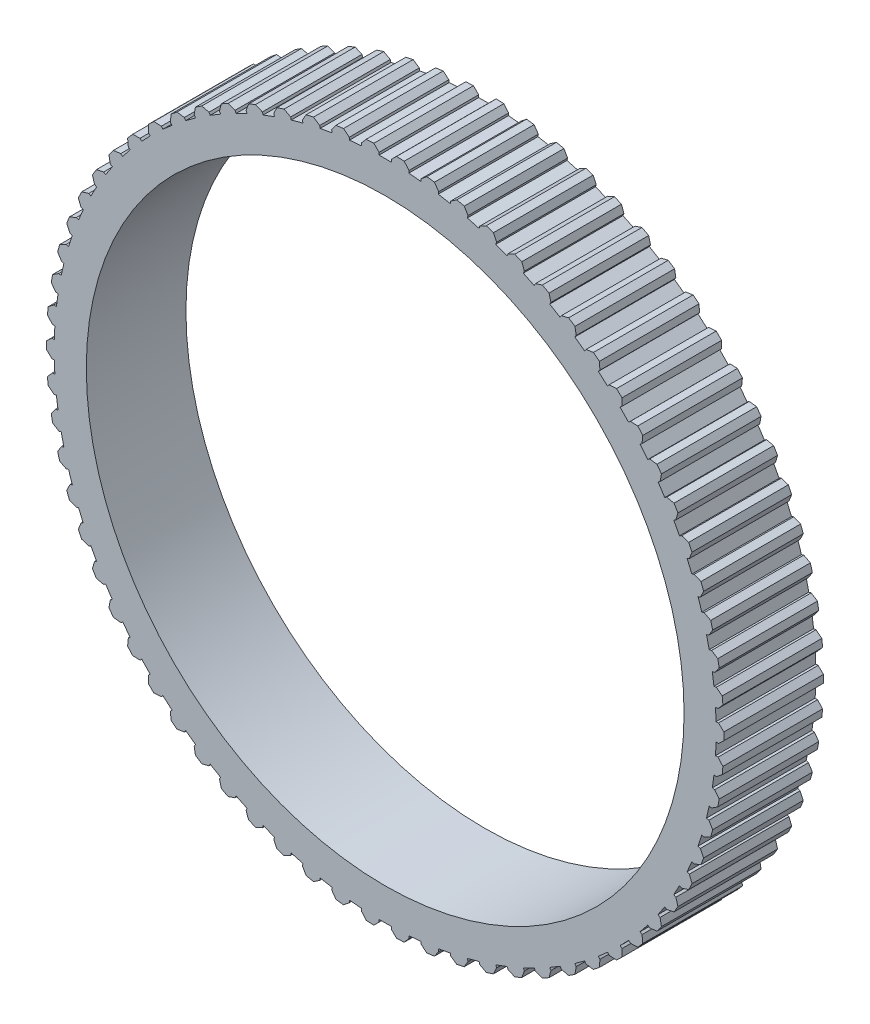
SolidWorks part; units mm, degrees
ref_plane "Front Plane" through (0, 0, 0) normal (0, 0, 1) x (1, 0, 0)
ref_plane "Top Plane" through (0, 0, 0) normal (0, 1, 0) x (1, 0, 0)
ref_plane "Right Plane" through (0, 0, 0) normal (1, 0, 0) x (0, 0, -1)
sketch "Sketch1" plane through (0, 0, 0) normal (0, 0, 1) x (1, 0, 0)
  line L0 (-2.86, 50.9197) -> (-3.5866, 50.0718)
  line L1 (-3.5866, 50.0718) -> (-3.5538, 49.707)
  line L2 (-3.5538, 49.707) -> (-5.3789, 49.5427)
  line L3 (-5.3789, 49.5427) -> (-5.4117, 49.9076)
  line L4 (-5.4117, 49.9076) -> (-6.2781, 50.6121)
  line L5 (-7.4129, 50.4584) -> (-8.0606, 49.5488)
  line L6 (-8.0606, 49.5488) -> (-7.9952, 49.1883)
  line L7 (-7.9952, 49.1883) -> (-9.7982, 48.8611)
  line L8 (-9.7982, 48.8611) -> (-9.8636, 49.2216)
  line L9 (-9.8636, 49.2216) -> (-10.7896, 49.8456)
  line L10 (-11.9061, 49.5908) -> (-12.4696, 48.6268)
  line L11 (-12.4696, 48.6268) -> (-12.3722, 48.2736)
  line L12 (-12.3722, 48.2736) -> (-14.1386, 47.7861)
  line L13 (-14.1386, 47.7861) -> (-14.2361, 48.1393)
  line L14 (-14.2361, 48.1393) -> (-15.2143, 48.6778)
  line L15 (-16.3034, 48.3239) -> (-16.7783, 47.3132)
  line L16 (-16.7783, 47.3132) -> (-16.6496, 46.9703)
  line L17 (-16.6496, 46.9703) -> (-18.3652, 46.3264)
  line L18 (-18.3652, 46.3264) -> (-18.4939, 46.6693)
  line L19 (-18.4939, 46.6693) -> (-19.5165, 47.118)
  line L20 (-20.5695, 46.6679) -> (-20.9519, 45.6188)
  line L21 (-20.9519, 45.6188) -> (-20.793, 45.2887)
  line L22 (-20.793, 45.2887) -> (-22.444, 44.4937)
  line L23 (-22.444, 44.4937) -> (-22.6029, 44.8237)
  line L24 (-22.6029, 44.8237) -> (-23.6616, 45.1789)
  line L25 (-24.67, 44.6362) -> (-24.9568, 43.557)
  line L26 (-24.9568, 43.557) -> (-24.7689, 43.2425)
  line L27 (-24.7689, 43.2425) -> (-26.342, 42.3027)
  line L28 (-26.342, 42.3027) -> (-26.5299, 42.6171)
  line L29 (-26.5299, 42.6171) -> (-27.6161, 42.876)
  line L30 (-28.5718, 42.2451) -> (-28.7607, 41.1445)
  line L31 (-28.7607, 41.1445) -> (-28.5454, 40.8482)
  line L32 (-28.5454, 40.8482) -> (-30.0279, 39.7711)
  line L33 (-30.0279, 39.7711) -> (-30.2432, 40.0674)
  line L34 (-30.2432, 40.0674) -> (-31.3483, 40.2279)
  line L35 (-32.2436, 39.5139) -> (-32.3331, 38.4008)
  line L36 (-32.3331, 38.4008) -> (-32.0921, 38.125)
  line L37 (-32.0921, 38.125) -> (-33.4721, 36.9193)
  line L38 (-33.4721, 36.9193) -> (-33.7131, 37.1952)
  line L39 (-33.7131, 37.1952) -> (-34.8281, 37.2559)
  line L40 (-35.6558, 36.4645) -> (-35.6452, 35.3479)
  line L41 (-35.6452, 35.3479) -> (-35.3804, 35.0948)
  line L42 (-35.3804, 35.0948) -> (-36.6468, 33.7703)
  line L43 (-36.6468, 33.7703) -> (-36.9115, 34.0234)
  line L44 (-36.9115, 34.0234) -> (-38.0275, 33.9839)
  line L45 (-38.7809, 33.1216) -> (-38.6702, 32.0104)
  line L46 (-38.6702, 32.0104) -> (-38.3839, 31.782)
  line L47 (-38.3839, 31.782) -> (-39.5264, 30.3493)
  line L48 (-39.5264, 30.3493) -> (-39.8128, 30.5777)
  line L49 (-39.8128, 30.5777) -> (-40.9207, 30.4384)
  line L50 (-41.5938, 29.5119) -> (-41.384, 28.4152)
  line L51 (-41.384, 28.4152) -> (-41.0782, 28.2134)
  line L52 (-41.0782, 28.2134) -> (-42.0877, 26.684)
  line L53 (-42.0877, 26.684) -> (-42.3935, 26.8858)
  line L54 (-42.3935, 26.8858) -> (-43.4845, 26.6477)
  line L55 (-44.0718, 25.6647) -> (-43.7645, 24.5911)
  line L56 (-43.7645, 24.5911) -> (-43.4419, 24.4176)
  line L57 (-43.4419, 24.4176) -> (-44.3103, 22.8039)
  line L58 (-44.3103, 22.8039) -> (-44.6328, 22.9775)
  line L59 (-44.6328, 22.9775) -> (-45.6981, 22.6425)
  line L60 (-46.1949, 21.6108) -> (-45.7926, 20.5691)
  line L61 (-45.7926, 20.5691) -> (-45.4558, 20.4252)
  line L62 (-45.4558, 20.4252) -> (-46.176, 18.7402)
  line L63 (-46.176, 18.7402) -> (-46.5128, 18.8841)
  line L64 (-46.5128, 18.8841) -> (-47.5438, 18.4551)
  line L65 (-47.9462, 17.3829) -> (-47.4521, 16.3815)
  line L66 (-47.4521, 16.3815) -> (-47.1037, 16.2683)
  line L67 (-47.1037, 16.2683) -> (-47.67, 14.5255)
  line L68 (-47.67, 14.5255) -> (-48.0183, 14.6387)
  line L69 (-48.0183, 14.6387) -> (-49.0067, 14.119)
  line L70 (-49.3113, 13.0151) -> (-48.7295, 12.062)
  line L71 (-48.7295, 12.062) -> (-48.3724, 11.9805)
  line L72 (-48.3724, 11.9805) -> (-48.7801, 10.1939)
  line L73 (-48.7801, 10.1939) -> (-49.1372, 10.2755)
  line L74 (-49.1372, 10.2755) -> (-50.075, 9.6692)
  line L75 (-50.2795, 8.5425) -> (-49.6145, 7.6453)
  line L76 (-49.6145, 7.6453) -> (-49.2515, 7.5962)
  line L77 (-49.2515, 7.5962) -> (-49.4975, 5.7803)
  line L78 (-49.4975, 5.7803) -> (-49.8605, 5.8295)
  line L79 (-49.8605, 5.8295) -> (-50.7402, 5.1416)
  line L80 (-50.8428, 4.001) -> (-50.1001, 3.1672)
  line L81 (-50.1001, 3.1672) -> (-49.7342, 3.1507)
  line L82 (-49.7342, 3.1507) -> (-49.8164, 1.3201)
  line L83 (-49.8164, 1.3201) -> (-50.1823, 1.3365)
  line L84 (-50.1823, 1.3365) -> (-50.9968, 0.5726)
  line L85 (-50.9968, -0.5726) -> (-50.1823, -1.3365)
  line L86 (-50.1823, -1.3365) -> (-49.8164, -1.3201)
  line L87 (-49.8164, -1.3201) -> (-49.7342, -3.1507)
  line L88 (-49.7342, -3.1507) -> (-50.1001, -3.1672)
  line L89 (-50.1001, -3.1672) -> (-50.8428, -4.001)
  line L90 (-50.7402, -5.1416) -> (-49.8605, -5.8295)
  line L91 (-49.8605, -5.8295) -> (-49.4975, -5.7803)
  line L92 (-49.4975, -5.7803) -> (-49.2515, -7.5962)
  line L93 (-49.2515, -7.5962) -> (-49.6145, -7.6453)
  line L94 (-49.6145, -7.6453) -> (-50.2795, -8.5425)
  line L95 (-50.075, -9.6692) -> (-49.1372, -10.2755)
  line L96 (-49.1372, -10.2755) -> (-48.7801, -10.1939)
  line L97 (-48.7801, -10.1939) -> (-48.3724, -11.9805)
  line L98 (-48.3724, -11.9805) -> (-48.7295, -12.062)
  line L99 (-48.7295, -12.062) -> (-49.3113, -13.0151)
  line L100 (-49.0067, -14.119) -> (-48.0183, -14.6387)
  line L101 (-48.0183, -14.6387) -> (-47.67, -14.5255)
  line L102 (-47.67, -14.5255) -> (-47.1037, -16.2683)
  line L103 (-47.1037, -16.2683) -> (-47.4521, -16.3815)
  line L104 (-47.4521, -16.3815) -> (-47.9462, -17.3829)
  line L105 (-47.5438, -18.4551) -> (-46.5128, -18.8841)
  line L106 (-46.5128, -18.8841) -> (-46.176, -18.7402)
  line L107 (-46.176, -18.7402) -> (-45.4558, -20.4252)
  line L108 (-45.4558, -20.4252) -> (-45.7926, -20.5691)
  line L109 (-45.7926, -20.5691) -> (-46.1949, -21.6108)
  line L110 (-45.6981, -22.6425) -> (-44.6328, -22.9775)
  line L111 (-44.6328, -22.9775) -> (-44.3103, -22.8039)
  line L112 (-44.3103, -22.8039) -> (-43.4419, -24.4176)
  line L113 (-43.4419, -24.4176) -> (-43.7645, -24.5911)
  line L114 (-43.7645, -24.5911) -> (-44.0718, -25.6647)
  line L115 (-43.4845, -26.6477) -> (-42.3935, -26.8858)
  line L116 (-42.3935, -26.8858) -> (-42.0877, -26.684)
  line L117 (-42.0877, -26.684) -> (-41.0782, -28.2134)
  line L118 (-41.0782, -28.2134) -> (-41.384, -28.4152)
  line L119 (-41.384, -28.4152) -> (-41.5938, -29.5119)
  line L120 (-40.9207, -30.4384) -> (-39.8128, -30.5777)
  line L121 (-39.8128, -30.5777) -> (-39.5264, -30.3493)
  line L122 (-39.5264, -30.3493) -> (-38.3839, -31.782)
  line L123 (-38.3839, -31.782) -> (-38.6702, -32.0104)
  line L124 (-38.6702, -32.0104) -> (-38.7809, -33.1216)
  line L125 (-38.0275, -33.9839) -> (-36.9115, -34.0234)
  line L126 (-36.9115, -34.0234) -> (-36.6468, -33.7703)
  line L127 (-36.6468, -33.7703) -> (-35.3804, -35.0948)
  line L128 (-35.3804, -35.0948) -> (-35.6452, -35.3479)
  line L129 (-35.6452, -35.3479) -> (-35.6558, -36.4645)
  line L130 (-34.8281, -37.2559) -> (-33.7131, -37.1952)
  line L131 (-33.7131, -37.1952) -> (-33.4721, -36.9193)
  line L132 (-33.4721, -36.9193) -> (-32.0921, -38.125)
  line L133 (-32.0921, -38.125) -> (-32.3331, -38.4008)
  line L134 (-32.3331, -38.4008) -> (-32.2436, -39.5139)
  line L135 (-31.3483, -40.2279) -> (-30.2432, -40.0674)
  line L136 (-30.2432, -40.0674) -> (-30.0279, -39.7711)
  line L137 (-30.0279, -39.7711) -> (-28.5454, -40.8482)
  line L138 (-28.5454, -40.8482) -> (-28.7607, -41.1445)
  line L139 (-28.7607, -41.1445) -> (-28.5718, -42.2451)
  line L140 (-27.6161, -42.876) -> (-26.5299, -42.6171)
  line L141 (-26.5299, -42.6171) -> (-26.342, -42.3027)
  line L142 (-26.342, -42.3027) -> (-24.7689, -43.2425)
  line L143 (-24.7689, -43.2425) -> (-24.9568, -43.557)
  line L144 (-24.9568, -43.557) -> (-24.67, -44.6362)
  line L145 (-23.6616, -45.1789) -> (-22.6029, -44.8237)
  line L146 (-22.6029, -44.8237) -> (-22.444, -44.4937)
  line L147 (-22.444, -44.4937) -> (-20.793, -45.2887)
  line L148 (-20.793, -45.2887) -> (-20.9519, -45.6188)
  line L149 (-20.9519, -45.6188) -> (-20.5695, -46.6679)
  line L150 (-19.5165, -47.118) -> (-18.4939, -46.6693)
  line L151 (-18.4939, -46.6693) -> (-18.3652, -46.3264)
  line L152 (-18.3652, -46.3264) -> (-16.6496, -46.9703)
  line L153 (-16.6496, -46.9703) -> (-16.7783, -47.3132)
  line L154 (-16.7783, -47.3132) -> (-16.3034, -48.3239)
  line L155 (-15.2143, -48.6778) -> (-14.2361, -48.1393)
  line L156 (-14.2361, -48.1393) -> (-14.1386, -47.7861)
  line L157 (-14.1386, -47.7861) -> (-12.3722, -48.2736)
  line L158 (-12.3722, -48.2736) -> (-12.4696, -48.6268)
  line L159 (-12.4696, -48.6268) -> (-11.9061, -49.5908)
  line L160 (-10.7896, -49.8456) -> (-9.8636, -49.2216)
  line L161 (-9.8636, -49.2216) -> (-9.7982, -48.8611)
  line L162 (-9.7982, -48.8611) -> (-7.9952, -49.1883)
  line L163 (-7.9952, -49.1883) -> (-8.0606, -49.5488)
  line L164 (-8.0606, -49.5488) -> (-7.4129, -50.4584)
  line L165 (-6.2781, -50.6121) -> (-5.4117, -49.9076)
  line L166 (-5.4117, -49.9076) -> (-5.3789, -49.5427)
  line L167 (-5.3789, -49.5427) -> (-3.5538, -49.707)
  line L168 (-3.5538, -49.707) -> (-3.5866, -50.0718)
  line L169 (-3.5866, -50.0718) -> (-2.86, -50.9197)
  line L170 (-1.716, -50.9711) -> (-0.9162, -50.1918)
  line L171 (-0.9162, -50.1918) -> (-0.9162, -49.8255)
  line L172 (-0.9162, -49.8255) -> (0.9162, -49.8255)
  line L173 (0.9162, -49.8255) -> (0.9162, -50.1918)
  line L174 (0.9162, -50.1918) -> (1.716, -50.9711)
  line L175 (2.86, -50.9197) -> (3.5866, -50.0718)
  line L176 (3.5866, -50.0718) -> (3.5538, -49.707)
  line L177 (3.5538, -49.707) -> (5.3789, -49.5427)
  line L178 (5.3789, -49.5427) -> (5.4117, -49.9076)
  line L179 (5.4117, -49.9076) -> (6.2781, -50.6121)
  line L180 (7.4129, -50.4584) -> (8.0606, -49.5488)
  line L181 (8.0606, -49.5488) -> (7.9952, -49.1883)
  line L182 (7.9952, -49.1883) -> (9.7982, -48.8611)
  line L183 (9.7982, -48.8611) -> (9.8636, -49.2216)
  line L184 (9.8636, -49.2216) -> (10.7896, -49.8456)
  line L185 (11.9061, -49.5908) -> (12.4696, -48.6268)
  line L186 (12.4696, -48.6268) -> (12.3722, -48.2736)
  line L187 (12.3722, -48.2736) -> (14.1386, -47.7861)
  line L188 (14.1386, -47.7861) -> (14.2361, -48.1393)
  line L189 (14.2361, -48.1393) -> (15.2143, -48.6778)
  line L190 (16.3034, -48.3239) -> (16.7783, -47.3132)
  line L191 (16.7783, -47.3132) -> (16.6496, -46.9703)
  line L192 (16.6496, -46.9703) -> (18.3652, -46.3264)
  line L193 (18.3652, -46.3264) -> (18.4939, -46.6693)
  line L194 (18.4939, -46.6693) -> (19.5165, -47.118)
  line L195 (20.5695, -46.6679) -> (20.9519, -45.6188)
  line L196 (20.9519, -45.6188) -> (20.793, -45.2887)
  line L197 (20.793, -45.2887) -> (22.444, -44.4937)
  line L198 (22.444, -44.4937) -> (22.6029, -44.8237)
  line L199 (22.6029, -44.8237) -> (23.6616, -45.1789)
  line L200 (24.67, -44.6362) -> (24.9568, -43.557)
  line L201 (24.9568, -43.557) -> (24.7689, -43.2425)
  line L202 (24.7689, -43.2425) -> (26.342, -42.3027)
  line L203 (26.342, -42.3027) -> (26.5299, -42.6171)
  line L204 (26.5299, -42.6171) -> (27.6161, -42.876)
  line L205 (28.5718, -42.2451) -> (28.7607, -41.1445)
  line L206 (28.7607, -41.1445) -> (28.5454, -40.8482)
  line L207 (28.5454, -40.8482) -> (30.0279, -39.7711)
  line L208 (30.0279, -39.7711) -> (30.2432, -40.0674)
  line L209 (30.2432, -40.0674) -> (31.3483, -40.2279)
  line L210 (32.2436, -39.5139) -> (32.3331, -38.4008)
  line L211 (32.3331, -38.4008) -> (32.0921, -38.125)
  line L212 (32.0921, -38.125) -> (33.4721, -36.9193)
  line L213 (33.4721, -36.9193) -> (33.7131, -37.1952)
  line L214 (33.7131, -37.1952) -> (34.8281, -37.2559)
  line L215 (35.6558, -36.4645) -> (35.6452, -35.3479)
  line L216 (35.6452, -35.3479) -> (35.3804, -35.0948)
  line L217 (35.3804, -35.0948) -> (36.6468, -33.7703)
  line L218 (36.6468, -33.7703) -> (36.9115, -34.0234)
  line L219 (36.9115, -34.0234) -> (38.0275, -33.9839)
  line L220 (38.7809, -33.1216) -> (38.6702, -32.0104)
  line L221 (38.6702, -32.0104) -> (38.3839, -31.782)
  line L222 (38.3839, -31.782) -> (39.5264, -30.3493)
  line L223 (39.5264, -30.3493) -> (39.8128, -30.5777)
  line L224 (39.8128, -30.5777) -> (40.9207, -30.4384)
  line L225 (41.5938, -29.5119) -> (41.384, -28.4152)
  line L226 (41.384, -28.4152) -> (41.0782, -28.2134)
  line L227 (41.0782, -28.2134) -> (42.0877, -26.684)
  line L228 (42.0877, -26.684) -> (42.3935, -26.8858)
  line L229 (42.3935, -26.8858) -> (43.4845, -26.6477)
  line L230 (44.0718, -25.6647) -> (43.7645, -24.5911)
  line L231 (43.7645, -24.5911) -> (43.4419, -24.4176)
  line L232 (43.4419, -24.4176) -> (44.3103, -22.8039)
  line L233 (44.3103, -22.8039) -> (44.6328, -22.9775)
  line L234 (44.6328, -22.9775) -> (45.6981, -22.6425)
  line L235 (46.1949, -21.6108) -> (45.7926, -20.5691)
  line L236 (45.7926, -20.5691) -> (45.4558, -20.4252)
  line L237 (45.4558, -20.4252) -> (46.176, -18.7402)
  line L238 (46.176, -18.7402) -> (46.5128, -18.8841)
  line L239 (46.5128, -18.8841) -> (47.5438, -18.4551)
  line L240 (47.9462, -17.3829) -> (47.4521, -16.3815)
  line L241 (47.4521, -16.3815) -> (47.1037, -16.2683)
  line L242 (47.1037, -16.2683) -> (47.67, -14.5255)
  line L243 (47.67, -14.5255) -> (48.0183, -14.6387)
  line L244 (48.0183, -14.6387) -> (49.0067, -14.119)
  line L245 (49.3113, -13.0151) -> (48.7295, -12.062)
  line L246 (48.7295, -12.062) -> (48.3724, -11.9805)
  line L247 (48.3724, -11.9805) -> (48.7801, -10.1939)
  line L248 (48.7801, -10.1939) -> (49.1372, -10.2755)
  line L249 (49.1372, -10.2755) -> (50.075, -9.6692)
  line L250 (50.2795, -8.5425) -> (49.6145, -7.6453)
  line L251 (49.6145, -7.6453) -> (49.2515, -7.5962)
  line L252 (49.2515, -7.5962) -> (49.4975, -5.7803)
  line L253 (49.4975, -5.7803) -> (49.8605, -5.8295)
  line L254 (49.8605, -5.8295) -> (50.7402, -5.1416)
  line L255 (50.8428, -4.001) -> (50.1001, -3.1672)
  line L256 (50.1001, -3.1672) -> (49.7342, -3.1507)
  line L257 (49.7342, -3.1507) -> (49.8164, -1.3201)
  line L258 (49.8164, -1.3201) -> (50.1823, -1.3365)
  line L259 (50.1823, -1.3365) -> (50.9968, -0.5726)
  line L260 (50.9968, 0.5726) -> (50.1823, 1.3365)
  line L261 (50.1823, 1.3365) -> (49.8164, 1.3201)
  line L262 (49.8164, 1.3201) -> (49.7342, 3.1507)
  line L263 (49.7342, 3.1507) -> (50.1001, 3.1672)
  line L264 (50.1001, 3.1672) -> (50.8428, 4.001)
  line L265 (50.7402, 5.1416) -> (49.8605, 5.8295)
  line L266 (49.8605, 5.8295) -> (49.4975, 5.7803)
  line L267 (49.4975, 5.7803) -> (49.2515, 7.5962)
  line L268 (49.2515, 7.5962) -> (49.6145, 7.6453)
  line L269 (49.6145, 7.6453) -> (50.2795, 8.5425)
  line L270 (50.075, 9.6692) -> (49.1372, 10.2755)
  line L271 (49.1372, 10.2755) -> (48.7801, 10.1939)
  line L272 (48.7801, 10.1939) -> (48.3724, 11.9805)
  line L273 (48.3724, 11.9805) -> (48.7295, 12.062)
  line L274 (48.7295, 12.062) -> (49.3113, 13.0151)
  line L275 (49.0067, 14.119) -> (48.0183, 14.6387)
  line L276 (48.0183, 14.6387) -> (47.67, 14.5255)
  line L277 (47.67, 14.5255) -> (47.1037, 16.2683)
  line L278 (47.1037, 16.2683) -> (47.4521, 16.3815)
  line L279 (47.4521, 16.3815) -> (47.9462, 17.3829)
  line L280 (47.5438, 18.4551) -> (46.5128, 18.8841)
  line L281 (46.5128, 18.8841) -> (46.176, 18.7402)
  line L282 (46.176, 18.7402) -> (45.4558, 20.4252)
  line L283 (45.4558, 20.4252) -> (45.7926, 20.5691)
  line L284 (45.7926, 20.5691) -> (46.1949, 21.6108)
  line L285 (45.6981, 22.6425) -> (44.6328, 22.9775)
  line L286 (44.6328, 22.9775) -> (44.3103, 22.8039)
  line L287 (44.3103, 22.8039) -> (43.4419, 24.4176)
  line L288 (43.4419, 24.4176) -> (43.7645, 24.5911)
  line L289 (43.7645, 24.5911) -> (44.0718, 25.6647)
  line L290 (43.4845, 26.6477) -> (42.3935, 26.8858)
  line L291 (42.3935, 26.8858) -> (42.0877, 26.684)
  line L292 (42.0877, 26.684) -> (41.0782, 28.2134)
  line L293 (41.0782, 28.2134) -> (41.384, 28.4152)
  line L294 (41.384, 28.4152) -> (41.5938, 29.5119)
  line L295 (40.9207, 30.4384) -> (39.8128, 30.5777)
  line L296 (39.8128, 30.5777) -> (39.5264, 30.3493)
  line L297 (39.5264, 30.3493) -> (38.3839, 31.782)
  line L298 (38.3839, 31.782) -> (38.6702, 32.0104)
  line L299 (38.6702, 32.0104) -> (38.7809, 33.1216)
  line L300 (38.0275, 33.9839) -> (36.9115, 34.0234)
  line L301 (36.9115, 34.0234) -> (36.6468, 33.7703)
  line L302 (36.6468, 33.7703) -> (35.3804, 35.0948)
  line L303 (35.3804, 35.0948) -> (35.6452, 35.3479)
  line L304 (35.6452, 35.3479) -> (35.6558, 36.4645)
  line L305 (34.8281, 37.2559) -> (33.7131, 37.1952)
  line L306 (33.7131, 37.1952) -> (33.4721, 36.9193)
  line L307 (33.4721, 36.9193) -> (32.0921, 38.125)
  line L308 (32.0921, 38.125) -> (32.3331, 38.4008)
  line L309 (32.3331, 38.4008) -> (32.2436, 39.5139)
  line L310 (31.3483, 40.2279) -> (30.2432, 40.0674)
  line L311 (30.2432, 40.0674) -> (30.0279, 39.7711)
  line L312 (30.0279, 39.7711) -> (28.5454, 40.8482)
  line L313 (28.5454, 40.8482) -> (28.7607, 41.1445)
  line L314 (28.7607, 41.1445) -> (28.5718, 42.2451)
  line L315 (27.6161, 42.876) -> (26.5299, 42.6171)
  line L316 (26.5299, 42.6171) -> (26.342, 42.3027)
  line L317 (26.342, 42.3027) -> (24.7689, 43.2425)
  line L318 (24.7689, 43.2425) -> (24.9568, 43.557)
  line L319 (24.9568, 43.557) -> (24.67, 44.6362)
  line L320 (23.6616, 45.1789) -> (22.6029, 44.8237)
  line L321 (22.6029, 44.8237) -> (22.444, 44.4937)
  line L322 (22.444, 44.4937) -> (20.793, 45.2887)
  line L323 (20.793, 45.2887) -> (20.9519, 45.6188)
  line L324 (20.9519, 45.6188) -> (20.5695, 46.6679)
  line L325 (19.5165, 47.118) -> (18.4939, 46.6693)
  line L326 (18.4939, 46.6693) -> (18.3652, 46.3264)
  line L327 (18.3652, 46.3264) -> (16.6496, 46.9703)
  line L328 (16.6496, 46.9703) -> (16.7783, 47.3132)
  line L329 (16.7783, 47.3132) -> (16.3034, 48.3239)
  line L330 (15.2143, 48.6778) -> (14.2361, 48.1393)
  line L331 (14.2361, 48.1393) -> (14.1386, 47.7861)
  line L332 (14.1386, 47.7861) -> (12.3722, 48.2736)
  line L333 (12.3722, 48.2736) -> (12.4696, 48.6268)
  line L334 (12.4696, 48.6268) -> (11.9061, 49.5908)
  line L335 (10.7896, 49.8456) -> (9.8636, 49.2216)
  line L336 (9.8636, 49.2216) -> (9.7982, 48.8611)
  line L337 (9.7982, 48.8611) -> (7.9952, 49.1883)
  line L338 (7.9952, 49.1883) -> (8.0606, 49.5488)
  line L339 (8.0606, 49.5488) -> (7.4129, 50.4584)
  line L340 (6.2781, 50.6121) -> (5.4117, 49.9076)
  line L341 (5.4117, 49.9076) -> (5.3789, 49.5427)
  line L342 (5.3789, 49.5427) -> (3.5538, 49.707)
  line L343 (3.5538, 49.707) -> (3.5866, 50.0718)
  line L344 (3.5866, 50.0718) -> (2.86, 50.9197)
  line L345 (1.716, 50.9711) -> (0.9162, 50.1918)
  line L346 (0.9162, 50.1918) -> (0.9162, 49.8255)
  line L347 (0.9162, 49.8255) -> (-0.9162, 49.8255)
  line L348 (-0.9162, 49.8255) -> (-0.9162, 50.1918)
  line L349 (-0.9162, 50.1918) -> (-1.716, 50.9711)
  circle A0 centre (0, 0) radius 45
  arc A1 (-6.2781, 50.6121) -> (-7.4129, 50.4584) centre (0, 0) ccw
  arc A2 (-10.7896, 49.8456) -> (-11.9061, 49.5908) centre (0, 0) ccw
  arc A3 (-15.2143, 48.6778) -> (-16.3034, 48.3239) centre (0, 0) ccw
  arc A4 (-19.5165, 47.118) -> (-20.5695, 46.6679) centre (0, 0) ccw
  arc A5 (-23.6616, 45.1789) -> (-24.67, 44.6362) centre (0, 0) ccw
  arc A6 (-27.6161, 42.876) -> (-28.5718, 42.2451) centre (0, 0) ccw
  arc A7 (-31.3483, 40.2279) -> (-32.2436, 39.5139) centre (0, 0) ccw
  arc A8 (-34.8281, 37.2559) -> (-35.6558, 36.4645) centre (0, 0) ccw
  arc A9 (-38.0275, 33.9839) -> (-38.7809, 33.1216) centre (0, 0) ccw
  arc A10 (-40.9207, 30.4384) -> (-41.5938, 29.5119) centre (0, 0) ccw
  arc A11 (-43.4845, 26.6477) -> (-44.0718, 25.6647) centre (0, 0) ccw
  arc A12 (-45.6981, 22.6425) -> (-46.1949, 21.6108) centre (0, 0) ccw
  arc A13 (-47.5438, 18.4551) -> (-47.9462, 17.3829) centre (0, 0) ccw
  arc A14 (-49.0067, 14.119) -> (-49.3113, 13.0151) centre (0, 0) ccw
  arc A15 (-50.075, 9.6692) -> (-50.2795, 8.5425) centre (0, 0) ccw
  arc A16 (-50.7402, 5.1416) -> (-50.8428, 4.001) centre (0, 0) ccw
  arc A17 (-50.9968, 0.5726) -> (-50.9968, -0.5726) centre (0, 0) ccw
  arc A18 (-50.8428, -4.001) -> (-50.7402, -5.1416) centre (0, 0) ccw
  arc A19 (-50.2795, -8.5425) -> (-50.075, -9.6692) centre (0, 0) ccw
  arc A20 (-49.3113, -13.0151) -> (-49.0067, -14.119) centre (0, 0) ccw
  arc A21 (-47.9462, -17.3829) -> (-47.5438, -18.4551) centre (0, 0) ccw
  arc A22 (-46.1949, -21.6108) -> (-45.6981, -22.6425) centre (0, 0) ccw
  arc A23 (-44.0718, -25.6647) -> (-43.4845, -26.6477) centre (0, 0) ccw
  arc A24 (-41.5938, -29.5119) -> (-40.9207, -30.4384) centre (0, 0) ccw
  arc A25 (-38.7809, -33.1216) -> (-38.0275, -33.9839) centre (0, 0) ccw
  arc A26 (-35.6558, -36.4645) -> (-34.8281, -37.2559) centre (0, 0) ccw
  arc A27 (-32.2436, -39.5139) -> (-31.3483, -40.2279) centre (0, 0) ccw
  arc A28 (-28.5718, -42.2451) -> (-27.6161, -42.876) centre (0, 0) ccw
  arc A29 (-24.67, -44.6362) -> (-23.6616, -45.1789) centre (0, 0) ccw
  arc A30 (-20.5695, -46.6679) -> (-19.5165, -47.118) centre (0, 0) ccw
  arc A31 (-16.3034, -48.3239) -> (-15.2143, -48.6778) centre (0, 0) ccw
  arc A32 (-11.9061, -49.5908) -> (-10.7896, -49.8456) centre (0, 0) ccw
  arc A33 (-7.4129, -50.4584) -> (-6.2781, -50.6121) centre (0, 0) ccw
  arc A34 (-2.86, -50.9197) -> (-1.716, -50.9711) centre (0, 0) ccw
  arc A35 (1.716, -50.9711) -> (2.86, -50.9197) centre (0, 0) ccw
  arc A36 (6.2781, -50.6121) -> (7.4129, -50.4584) centre (0, 0) ccw
  arc A37 (10.7896, -49.8456) -> (11.9061, -49.5908) centre (0, 0) ccw
  arc A38 (15.2143, -48.6778) -> (16.3034, -48.3239) centre (0, 0) ccw
  arc A39 (19.5165, -47.118) -> (20.5695, -46.6679) centre (0, 0) ccw
  arc A40 (23.6616, -45.1789) -> (24.67, -44.6362) centre (0, 0) ccw
  arc A41 (27.6161, -42.876) -> (28.5718, -42.2451) centre (0, 0) ccw
  arc A42 (31.3483, -40.2279) -> (32.2436, -39.5139) centre (0, 0) ccw
  arc A43 (34.8281, -37.2559) -> (35.6558, -36.4645) centre (0, 0) ccw
  arc A44 (38.0275, -33.9839) -> (38.7809, -33.1216) centre (0, 0) ccw
  arc A45 (40.9207, -30.4384) -> (41.5938, -29.5119) centre (0, 0) ccw
  arc A46 (43.4845, -26.6477) -> (44.0718, -25.6647) centre (0, 0) ccw
  arc A47 (45.6981, -22.6425) -> (46.1949, -21.6108) centre (0, 0) ccw
  arc A48 (47.5438, -18.4551) -> (47.9462, -17.3829) centre (0, 0) ccw
  arc A49 (49.0067, -14.119) -> (49.3113, -13.0151) centre (0, 0) ccw
  arc A50 (50.075, -9.6692) -> (50.2795, -8.5425) centre (0, 0) ccw
  arc A51 (50.7402, -5.1416) -> (50.8428, -4.001) centre (0, 0) ccw
  arc A52 (50.9968, -0.5726) -> (50.9968, 0.5726) centre (0, 0) ccw
  arc A53 (50.8428, 4.001) -> (50.7402, 5.1416) centre (0, 0) ccw
  arc A54 (50.2795, 8.5425) -> (50.075, 9.6692) centre (0, 0) ccw
  arc A55 (49.3113, 13.0151) -> (49.0067, 14.119) centre (0, 0) ccw
  arc A56 (47.9462, 17.3829) -> (47.5438, 18.4551) centre (0, 0) ccw
  arc A57 (46.1949, 21.6108) -> (45.6981, 22.6425) centre (0, 0) ccw
  arc A58 (44.0718, 25.6647) -> (43.4845, 26.6477) centre (0, 0) ccw
  arc A59 (41.5938, 29.5119) -> (40.9207, 30.4384) centre (0, 0) ccw
  arc A60 (38.7809, 33.1216) -> (38.0275, 33.9839) centre (0, 0) ccw
  arc A61 (35.6558, 36.4645) -> (34.8281, 37.2559) centre (0, 0) ccw
  arc A62 (32.2436, 39.5139) -> (31.3483, 40.2279) centre (0, 0) ccw
  arc A63 (28.5718, 42.2451) -> (27.6161, 42.876) centre (0, 0) ccw
  arc A64 (24.67, 44.6362) -> (23.6616, 45.1789) centre (0, 0) ccw
  arc A65 (20.5695, 46.6679) -> (19.5165, 47.118) centre (0, 0) ccw
  arc A66 (16.3034, 48.3239) -> (15.2143, 48.6778) centre (0, 0) ccw
  arc A67 (11.9061, 49.5908) -> (10.7896, 49.8456) centre (0, 0) ccw
  arc A68 (7.4129, 50.4584) -> (6.2781, 50.6121) centre (0, 0) ccw
  arc A69 (2.86, 50.9197) -> (1.716, 50.9711) centre (0, 0) ccw
  arc A70 (-1.716, 50.9711) -> (-2.86, 50.9197) centre (0, 0) ccw
extrude "Boss-Extrude1" add sketch "Sketch1" along normal blind 15 contours L349 A70 L0 L1 L2 L3 L4 A1 L5 L6 L7 L8 L9 A2 L10 L11 L12 L13 L14 A3 L15 L16 L17 L18 L19 A4 L20 L21 L22 L23 L24 A5 L25 L26 L27 L28 L29 A6 L30 L31 L32 L33 L34 A7 L35 L36 L37 L38 L39 A8 L40
